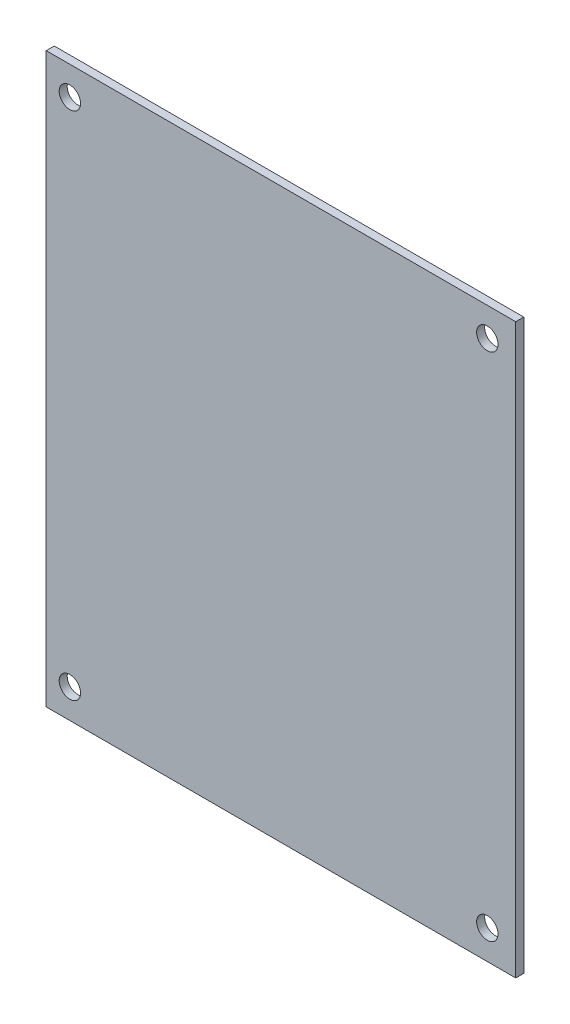
SolidWorks part; units mm, degrees
ref_plane "Front Plane" through (0, 0, 0) normal (0, 0, 1) x (1, 0, 0)
ref_plane "Top Plane" through (0, 0, 0) normal (0, 1, 0) x (1, 0, 0)
ref_plane "Right Plane" through (0, 0, 0) normal (1, 0, 0) x (0, 0, -1)
sketch "Sketch1" plane through (0, 0, 0) normal (0, 0, 1) x (1, 0, 0)
  line L1 (0, 0) -> (87.72, 0)
  line L2 (0, 0) -> (0, 106.2)
  line L3 (0, 106.2) -> (87.72, 106.2)
  line L4 (87.72, 0) -> (87.72, 106.2)
  dimension "D1" = 106.2
  dimension "D2" = 87.72
extrude "Boss-Extrude1" add sketch "Sketch1" along normal blind 1.5
sketch "Sketch2" plane through (0, 0, 1.5) normal (0, 0, 1) x (1, 0, 0)
  circle A0 centre (4.4132, 100.8511) radius 2
  circle A1 centre (4.4132, 5.4511) radius 2
  circle A2 centre (82.4132, 100.8511) radius 2
  circle A3 centre (82.4132, 5.4511) radius 2
  point P8 (0, 0)
  point P9 (4.4132, 5.4511)
  dimension "D1" = 4
  dimension "D2" = 4
  dimension "D3" = 95.4
  dimension "D4" = 4
  dimension "D5" = 78
  dimension "D6" = 78
extrude "Cut-Extrude1" cut sketch "Sketch2" against normal through all
